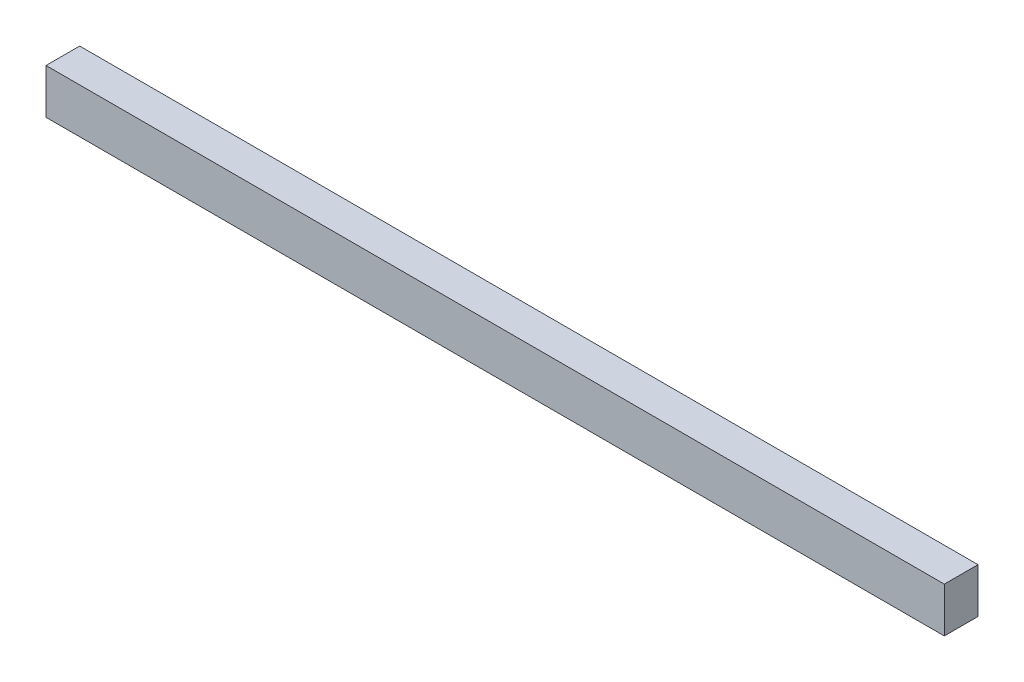
SolidWorks part; units mm, degrees
material "Oak"
ref_plane "Front Plane" through (0, 0, 0) normal (0, 0, 1) x (1, 0, 0)
ref_plane "Top Plane" through (0, 0, 0) normal (0, 1, 0) x (1, 0, 0)
ref_plane "Right Plane" through (0, 0, 0) normal (1, 0, 0) x (0, 0, -1)
sketch "Sketch1" plane through (0, 0, 0) normal (0, 0, 1) x (1, 0, 0)
  line L1 (-200, -10) -> (200, -10)
  line L2 (-200, -10) -> (-200, 10)
  line L3 (-200, 10) -> (200, 10)
  line L4 (200, -10) -> (200, 10)
  line L5 (-200, -10) -> (200, 10) construction
  line L6 (-200, 10) -> (200, -10) construction
  point P0 (0, 0)
  dimension "D1" = 20
  dimension "D2" = 400
extrude "Boss-Extrude1" add sketch "Sketch1" along normal mid plane 15
sketch "Sketch2" plane through (0, 0, -7.5) normal (0, 0, -1) x (-1, 0, 0)
  line L0 (-185, 10) -> (-185, -10) construction
  line L1 (-200, 10) -> (200, 10) construction
  line L2 (200, -10) -> (-200, -10) construction
  line L3 (-185, 10) -> (-200, 10) construction
  line L4 (-192.5, 10) -> (-192.5, -10) construction
  circle A0 centre (-192.5, 0) radius 4
  dimension "D1" = 15
  dimension "D2" = 8
extrude "Cut-Extrude1" cut sketch "Sketch2" against normal blind 10
mirror "Mirror1" about plane through (0, 0, 0) normal (1, 0, 0) of "Cut-Extrude1"
equation "\"A\"= 20mm"
equation "\"B\"= 400mm"
equation "\"C\"= 15mm"
equation "\"D1@Sketch1\"=\"A\""
equation "\"D2@Sketch1\"=\"B\""
equation "\"D1@Boss-Extrude1\"=\"C\""
equation "\"D1@Sketch2\"=\"C\""
